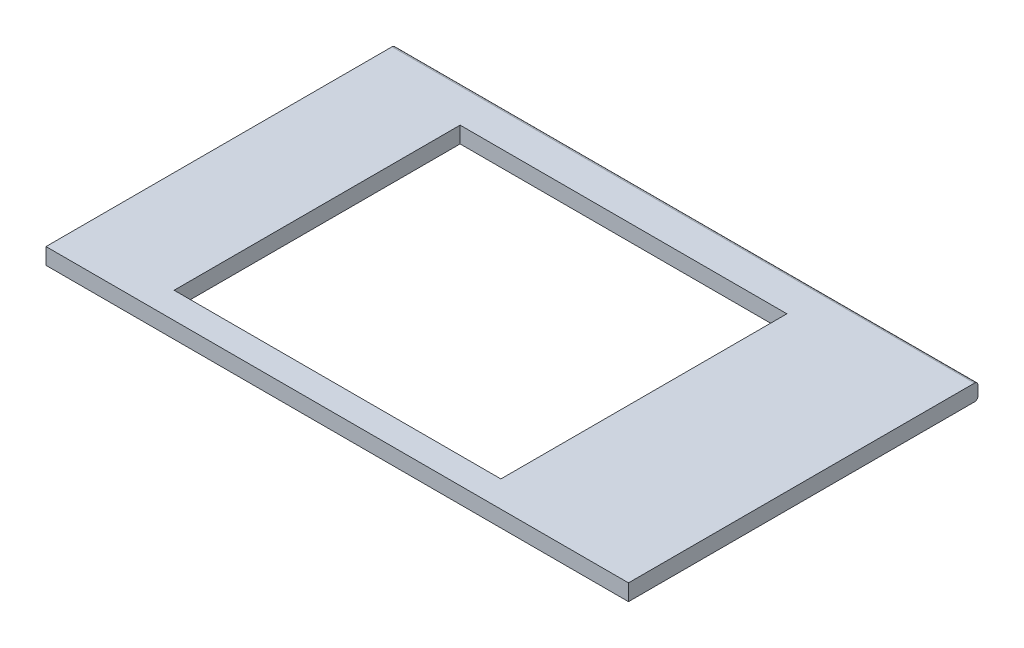
SolidWorks part; units mm, degrees
ref_plane "Спереди" through (0, 0, 0) normal (0, 0, 1) x (1, 0, 0)
ref_plane "Сверху" through (0, 0, 0) normal (0, 1, 0) x (1, 0, 0)
ref_plane "Справа" through (0, 0, 0) normal (1, 0, 0) x (0, 0, -1)
sketch "Эскиз2" plane through (0, 0, 0) normal (1, 0, 0) x (0, 0, -1)
  line L0 (0, 0) -> (594, 0)
  line L1 (0, 0) -> (0, 28)
  line L2 (0, 28) -> (594, 28)
  line L3 (600, 22) -> (600, 6)
  arc A1 (594, 0) -> (600, 6) centre (594, 6) ccw
  arc A2 (600, 22) -> (594, 28) centre (594, 22) ccw
  dimension "D1" = 6
extrude "Бобышка-Вытянуть1" add sketch "Эскиз2" along normal blind 1000
sketch "Эскиз3" plane through (0, 28, 0) normal (0, 1, 0) x (1, 0, 0)
  line L1 (174.9384, 536) -> (735.9384, 536)
  line L2 (174.9384, 536) -> (174.9384, 45)
  line L3 (174.9384, 45) -> (735.9384, 45)
  line L4 (735.9384, 536) -> (735.9384, 45)
  point P4 (0, 0)
  point P5 (0, 0)
  point P6 (0, 0)
  dimension "D1" = 491
  dimension "D2" = 561
extrude "Вырез-Вытянуть1" cut sketch "Эскиз3" against normal through all
